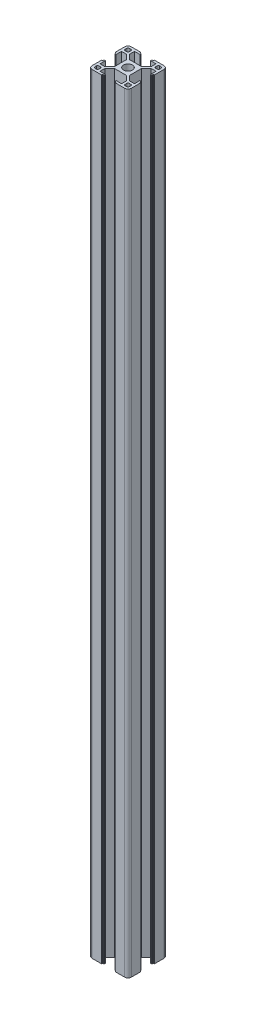
SolidWorks part; units mm, degrees
material "6063-T5"
ref_plane "前视基准面" through (0, 0, 0) normal (0, 0, 1) x (1, 0, 0)
ref_plane "上视基准面" through (0, 0, 0) normal (0, 1, 0) x (1, 0, 0)
ref_plane "右视基准面" through (0, 0, 0) normal (1, 0, 0) x (0, 0, -1)
sketch "草图3" plane through (0, 0, 0) normal (0, 1, 0) x (1, 0, 0)
  line L0 (0, 0) -> (-15, -15) construction
  line L1 (-15, -15) -> (-15, 0) construction
  line L2 (-15, 0) -> (0, 0) construction
  line L3 (-15, -12.5) -> (-15, -5.4)
  line L4 (-14.8, -5.2) -> (-14.4, -5.2)
  line L5 (-14.2, -5) -> (-14.2, -4.3)
  line L6 (-14, -4.1) -> (-13.2, -4.1)
  line L7 (-13.2, -4.1) -> (-13.2, -8.25)
  line L8 (-13.2, -8.25) -> (-9.5228, -8.25)
  line L9 (-9.5228, -8.25) -> (-5.8, -4.5272)
  line L10 (-5.8, -4.5272) -> (-5.8, 4.5272)
  line L11 (-13.2, -12.2) -> (-13.2, -11.05)
  line L12 (-12.2, -10.05) -> (-11.05, -10.05)
  line L13 (-4.5272, -5.8) -> (4.5272, -5.8)
  line L14 (-8.25, -9.5228) -> (-4.5272, -5.8)
  line L15 (-12.2, -13.2) -> (-11.05, -13.2)
  line L16 (-10.05, -12.2) -> (-10.05, -11.05)
  line L17 (-5.2, -14.8) -> (-5.2, -14.4)
  line L18 (-5, -14.2) -> (-4.3, -14.2)
  line L19 (-4.1, -14) -> (-4.1, -13.2)
  line L20 (-4.1, -13.2) -> (-8.25, -13.2)
  line L21 (-8.25, -13.2) -> (-8.25, -9.5228)
  line L22 (-12.5, -15) -> (-5.4, -15)
  line L23 (-12.5, 15) -> (-5.4, 15)
  line L24 (-8.25, 13.2) -> (-8.25, 9.5228)
  line L25 (-4.1, 13.2) -> (-8.25, 13.2)
  line L26 (-4.1, 14) -> (-4.1, 13.2)
  line L27 (-5, 14.2) -> (-4.3, 14.2)
  line L28 (-5.2, 14.8) -> (-5.2, 14.4)
  line L29 (-10.05, 12.2) -> (-10.05, 11.05)
  line L30 (-12.2, 13.2) -> (-11.05, 13.2)
  line L31 (-8.25, 9.5228) -> (-4.5272, 5.8)
  line L32 (-4.5272, 5.8) -> (4.5272, 5.8)
  line L33 (-12.2, 10.05) -> (-11.05, 10.05)
  line L34 (-13.2, 12.2) -> (-13.2, 11.05)
  line L35 (-9.5228, 8.25) -> (-5.8, 4.5272)
  line L36 (-13.2, 8.25) -> (-9.5228, 8.25)
  line L37 (-13.2, 4.1) -> (-13.2, 8.25)
  line L38 (-14, 4.1) -> (-13.2, 4.1)
  line L39 (-14.2, 5) -> (-14.2, 4.3)
  line L40 (-14.8, 5.2) -> (-14.4, 5.2)
  line L41 (-15, 12.5) -> (-15, 5.4)
  line L42 (0, 0) -> (0, -12.3268) construction
  line L43 (15, 12.5) -> (15, 5.4)
  line L44 (14.8, 5.2) -> (14.4, 5.2)
  line L45 (14.2, 5) -> (14.2, 4.3)
  line L46 (14, 4.1) -> (13.2, 4.1)
  line L47 (13.2, 4.1) -> (13.2, 8.25)
  line L48 (13.2, 8.25) -> (9.5228, 8.25)
  line L49 (9.5228, 8.25) -> (5.8, 4.5272)
  line L50 (13.2, 12.2) -> (13.2, 11.05)
  line L51 (12.2, 10.05) -> (11.05, 10.05)
  line L52 (8.25, 9.5228) -> (4.5272, 5.8)
  line L53 (12.2, 13.2) -> (11.05, 13.2)
  line L54 (10.05, 12.2) -> (10.05, 11.05)
  line L55 (5.2, 14.8) -> (5.2, 14.4)
  line L56 (5, 14.2) -> (4.3, 14.2)
  line L57 (4.1, 14) -> (4.1, 13.2)
  line L58 (4.1, 13.2) -> (8.25, 13.2)
  line L59 (8.25, 13.2) -> (8.25, 9.5228)
  line L60 (12.5, 15) -> (5.4, 15)
  line L61 (12.5, -15) -> (5.4, -15)
  line L62 (8.25, -13.2) -> (8.25, -9.5228)
  line L63 (4.1, -13.2) -> (8.25, -13.2)
  line L64 (4.1, -14) -> (4.1, -13.2)
  line L65 (5, -14.2) -> (4.3, -14.2)
  line L66 (5.2, -14.8) -> (5.2, -14.4)
  line L67 (10.05, -12.2) -> (10.05, -11.05)
  line L68 (12.2, -13.2) -> (11.05, -13.2)
  line L69 (8.25, -9.5228) -> (4.5272, -5.8)
  line L70 (12.2, -10.05) -> (11.05, -10.05)
  line L71 (13.2, -12.2) -> (13.2, -11.05)
  line L72 (5.8, -4.5272) -> (5.8, 4.5272)
  line L73 (9.5228, -8.25) -> (5.8, -4.5272)
  line L74 (13.2, -8.25) -> (9.5228, -8.25)
  line L75 (13.2, -4.1) -> (13.2, -8.25)
  line L76 (14, -4.1) -> (13.2, -4.1)
  line L77 (14.2, -5) -> (14.2, -4.3)
  line L78 (14.8, -5.2) -> (14.4, -5.2)
  line L79 (15, -12.5) -> (15, -5.4)
  circle A0 centre (0, 0) radius 3.4
  arc A1 (-12.5, 15) -> (-15, 12.5) centre (-12.5, 12.5) ccw
  arc A2 (15, 12.5) -> (12.5, 15) centre (12.5, 12.5) ccw
  arc A3 (12.5, -15) -> (15, -12.5) centre (12.5, -12.5) ccw
  arc A4 (-15, -12.5) -> (-12.5, -15) centre (-12.5, -12.5) ccw
  arc A5 (-12.2, 13.2) -> (-13.2, 12.2) centre (-12.2, 12.2) ccw
  arc A6 (-12.2, 10.05) -> (-13.2, 11.05) centre (-12.2, 11.05) cw
  arc A7 (-10.05, 11.05) -> (-11.05, 10.05) centre (-11.05, 11.05) cw
  arc A8 (-10.05, 12.2) -> (-11.05, 13.2) centre (-11.05, 12.2) ccw
  arc A9 (11.05, 10.05) -> (10.05, 11.05) centre (11.05, 11.05) cw
  arc A10 (11.05, 13.2) -> (10.05, 12.2) centre (11.05, 12.2) ccw
  arc A11 (13.2, 12.2) -> (12.2, 13.2) centre (12.2, 12.2) ccw
  arc A12 (13.2, 11.05) -> (12.2, 10.05) centre (12.2, 11.05) cw
  arc A13 (12.2, -10.05) -> (13.2, -11.05) centre (12.2, -11.05) cw
  arc A14 (10.05, -11.05) -> (11.05, -10.05) centre (11.05, -11.05) cw
  arc A15 (10.05, -12.2) -> (11.05, -13.2) centre (11.05, -12.2) ccw
  arc A16 (12.2, -13.2) -> (13.2, -12.2) centre (12.2, -12.2) ccw
  arc A17 (-13.2, -11.05) -> (-12.2, -10.05) centre (-12.2, -11.05) cw
  arc A18 (-11.05, -10.05) -> (-10.05, -11.05) centre (-11.05, -11.05) cw
  arc A19 (-11.05, -13.2) -> (-10.05, -12.2) centre (-11.05, -12.2) ccw
  arc A20 (-13.2, -12.2) -> (-12.2, -13.2) centre (-12.2, -12.2) ccw
  arc A21 (-15, -5.4) -> (-14.8, -5.2) centre (-14.8, -5.4) cw
  arc A22 (-14.4, -5.2) -> (-14.2, -5) centre (-14.4, -5) ccw
  arc A23 (-14.2, -4.3) -> (-14, -4.1) centre (-14, -4.3) cw
  arc A24 (-14, 4.1) -> (-14.2, 4.3) centre (-14, 4.3) cw
  arc A25 (-14.2, 5) -> (-14.4, 5.2) centre (-14.4, 5) ccw
  arc A26 (-14.8, 5.2) -> (-15, 5.4) centre (-14.8, 5.4) cw
  arc A27 (-5.4, 15) -> (-5.2, 14.8) centre (-5.4, 14.8) cw
  arc A28 (-5, 14.2) -> (-5.2, 14.4) centre (-5, 14.4) cw
  arc A29 (-4.1, 14) -> (-4.3, 14.2) centre (-4.3, 14) ccw
  arc A30 (5.2, 14.8) -> (5.4, 15) centre (5.4, 14.8) cw
  arc A31 (5.2, 14.4) -> (5, 14.2) centre (5, 14.4) cw
  arc A32 (4.3, 14.2) -> (4.1, 14) centre (4.3, 14) ccw
  arc A33 (15, 5.4) -> (14.8, 5.2) centre (14.8, 5.4) cw
  arc A34 (14.4, 5.2) -> (14.2, 5) centre (14.4, 5) ccw
  arc A35 (14.2, 4.3) -> (14, 4.1) centre (14, 4.3) cw
  arc A36 (14, -4.1) -> (14.2, -4.3) centre (14, -4.3) cw
  arc A37 (14.2, -5) -> (14.4, -5.2) centre (14.4, -5) ccw
  arc A38 (14.8, -5.2) -> (15, -5.4) centre (14.8, -5.4) cw
  arc A39 (5.4, -15) -> (5.2, -14.8) centre (5.4, -14.8) cw
  arc A40 (5, -14.2) -> (5.2, -14.4) centre (5, -14.4) cw
  arc A41 (4.1, -14) -> (4.3, -14.2) centre (4.3, -14) ccw
  arc A42 (-5.2, -14.4) -> (-5, -14.2) centre (-5, -14.4) cw
  arc A43 (-4.3, -14.2) -> (-4.1, -14) centre (-4.3, -14) ccw
  arc A44 (-5.2, -14.8) -> (-5.4, -15) centre (-5.4, -14.8) cw
  point P38 (-5.8, 0)
  point P46 (0, 5.8)
  point P47 (0, -5.8)
  point P83 (5.8, 0)
  point P87 (-15, 15)
  point P90 (15, 15)
  point P93 (15, -15)
  point P99 (-13.2, 13.2)
  point P102 (-13.2, 10.05)
  point P105 (-10.05, 10.05)
  point P108 (-10.05, 13.2)
  point P111 (10.05, 10.05)
  point P114 (10.05, 13.2)
  point P117 (13.2, 13.2)
  point P120 (13.2, 10.05)
  point P123 (13.2, -10.05)
  point P126 (10.05, -10.05)
  point P129 (10.05, -13.2)
  point P132 (13.2, -13.2)
  point P135 (-13.2, -10.05)
  point P138 (-10.05, -10.05)
  point P141 (-10.05, -13.2)
  point P144 (-13.2, -13.2)
  point P147 (-15, -5.2)
  point P150 (-14.2, -5.2)
  point P153 (-14.2, -4.1)
  point P156 (-14.2, 4.1)
  point P159 (-14.2, 5.2)
  point P162 (-15, 5.2)
  point P165 (-5.2, 15)
  point P168 (-5.2, 14.2)
  point P171 (-4.1, 14.2)
  point P174 (5.2, 15)
  point P177 (5.2, 14.2)
  point P180 (4.1, 14.2)
  point P183 (15, 5.2)
  point P186 (14.2, 5.2)
  point P189 (14.2, 4.1)
  point P192 (14.2, -4.1)
  point P195 (14.2, -5.2)
  point P198 (15, -5.2)
  point P201 (5.2, -15)
  point P204 (5.2, -14.2)
  point P207 (4.1, -14.2)
  point P210 (-5.2, -14.2)
  point P213 (-4.1, -14.2)
  point P216 (-5.2, -15)
  dimension "D11" = 6.8
  dimension "D12" = 2.5
  dimension "D13" = 1
  dimension "D14" = 0.2
  dimension "D2" = 15
  dimension "D3" = 4.1
  dimension "D4" = 5.2
  dimension "D5" = 0.8
  dimension "D6" = 1.8
  dimension "D7" = 9.2
  dimension "D8" = 8.25
  dimension "D9" = 0.9
  dimension "D10" = 1.8
extrude "凸台-拉伸1" add sketch "草图3" along normal blind 589
ref_plane "基准面1" through (-10.05, 294.5, 12.2) normal (0, -1, 0) x (-1, 0, 0)
sketch "草图4" plane through (0, 0, -5.8) normal (0, 0, -1) x (-1, 0, 0)
  line L0 (5.4, 589) -> (12.5, 589) construction
  line L1 (5.4, 0) -> (12.5, 0) construction
  circle A1 centre (0, 439) radius 3
  circle A2 centre (0, 150) radius 3
  dimension "D2" = 6
  dimension "D3" = 6
  dimension "D4" = 150
  dimension "D5" = 150
extrude "切除-拉伸1" cut sketch "草图4" against normal blind 87
